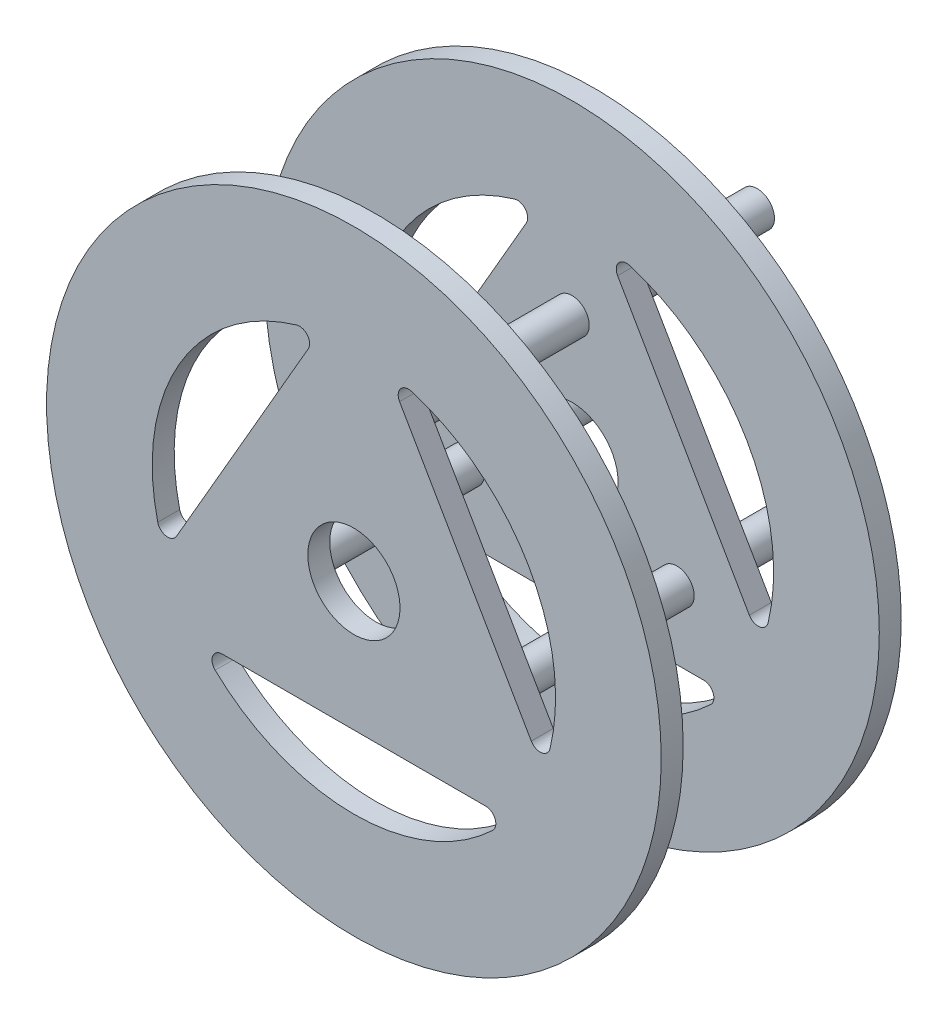
SolidWorks part; units mm, degrees
ref_plane "Front Plane" through (0, 0, 0) normal (0, 0, 1) x (1, 0, 0)
ref_plane "Top Plane" through (0, 0, 0) normal (0, 1, 0) x (1, 0, 0)
ref_plane "Right Plane" through (0, 0, 0) normal (1, 0, 0) x (0, 0, -1)
sketch "Sketch1" plane through (0, 0, 0) normal (0, 0, 1) x (1, 0, 0)
  circle A1 centre (0, 0) radius 26.67
  dimension "D1" = 53.34
extrude "Boss-Extrude1" add sketch "Sketch1" along normal blind 20.828
ref_plane "Plane1" through (0, 0, 10.414) normal (0, 0, 1) x (1, 0, 0)
sketch "Sketch4" plane through (0, 0, 0) normal (0, 0, -1) x (-1, 0, 0)
  line L0 (-3.9628, 15.4862) -> (-15.3928, -4.3112)
  line L4 (15.3928, -4.3112) -> (3.9628, 15.4862)
  line L5 (-11.43, -11.175) -> (11.43, -11.175)
  line L8 (0, 10.517) -> (0, 0) construction
  circle A0 centre (0, 0) radius 17.5 construction
  arc A1 (-17.019, -4.0749) -> (-4.9805, 16.7763) centre (0, 0) cw
  arc A4 (-15.3928, -4.3112) -> (-17.019, -4.0749) centre (-16.1588, -3.8689) cw
  arc A5 (-3.9628, 15.4862) -> (-4.9805, 16.7763) centre (-4.7288, 15.9284) ccw
  circle A10 centre (0, 0) radius 3.175 construction
  circle A11 centre (0, 10.517) radius 1.5
  circle A12 centre (9.108, -5.2585) radius 1.5
  arc A13 (4.9805, 16.7763) -> (17.019, -4.0749) centre (0, 0) cw
  arc A14 (15.3928, -4.3112) -> (17.019, -4.0749) centre (16.1588, -3.8689) ccw
  arc A15 (3.9628, 15.4862) -> (4.9805, 16.7763) centre (4.7288, 15.9284) cw
  circle A16 centre (-9.108, -5.2585) radius 1.5
  arc A17 (12.0384, -12.7014) -> (-12.0384, -12.7014) centre (0, 0) cw
  arc A18 (-11.43, -11.175) -> (-12.0384, -12.7014) centre (-11.43, -12.0595) ccw
  arc A19 (11.43, -11.175) -> (12.0384, -12.7014) centre (11.43, -12.0595) cw
  circle A20 centre (0, 0) radius 4
  circle A21 centre (0, 0) radius 4 construction
  circle A22 centre (0, 0) radius 4 construction
  point P3 (3.8443, 15.9284)
  point P5 (0, 17.5)
  point P18 (-3.8443, 15.9284)
  point P19 (0, 17.5)
  point P30 (0, 9.017)
  point P31 (0, 3.175)
  point P33 (0, -3.175)
  point P36 (0, 0)
  point P37 (0, -4)
  point P38 (0, -4)
  point P44 (0, -17.5)
  point P47 (0, -17.5)
  point P48 (0, -11.175)
  dimension "D1" = 35
  dimension "D2" = 6.35
  dimension "D3" = 3
  dimension "D4" = 5.842
  dimension "D5" = 3
  dimension "D6" = 8
  dimension "D7" = 8
extrude "Cut-Extrude2" cut sketch "Sketch4" against normal through all
sketch "Sketch5" plane through (0, 0, 0) normal (0, 0, -1) x (-1, 0, 0)
  circle A0 centre (0, 0) radius 26.67
extrude "Cut-Extrude3" cut sketch "Sketch5" against normal mid plane 17.018 from surface at -10.414 starting at plane "Plane1"
sketch "Sketch9" plane through (0, 0, 10.414) normal (0, 0, 1) x (1, 0, 0)
  circle A6 centre (0, 10.517) radius 1.5
  circle A7 centre (9.108, -5.2585) radius 1.5
  circle A8 centre (-9.108, -5.2585) radius 1.5
  point P12 (0, 0)
  dimension "D1" = 3
  dimension "D2" = 3
extrude "Boss-Extrude2" add sketch "Sketch9" against normal blind 35 from surface at 10.414 starting at face at (-4, 0, 20.828)
